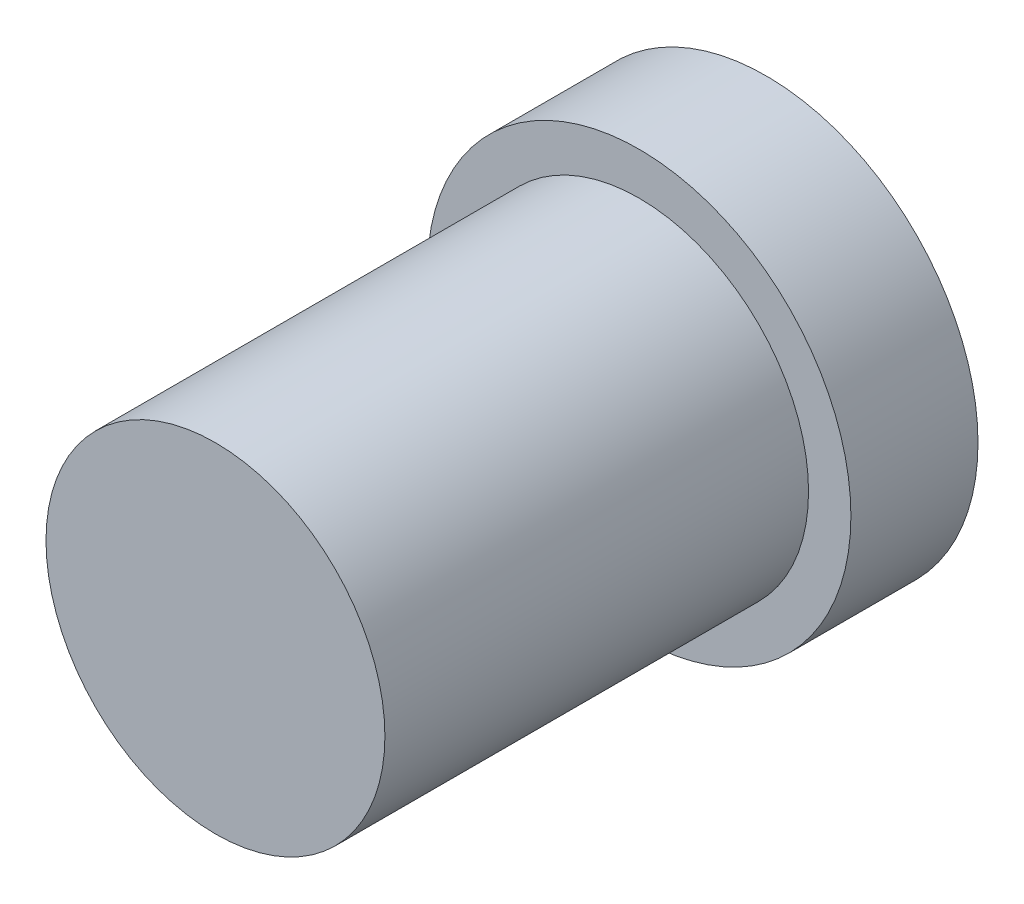
SolidWorks part; units mm, degrees
ref_plane "Front Plane" through (0, 0, 0) normal (0, 0, 1) x (1, 0, 0)
ref_plane "Top Plane" through (0, 0, 0) normal (0, 1, 0) x (1, 0, 0)
ref_plane "Right Plane" through (0, 0, 0) normal (1, 0, 0) x (0, 0, -1)
sketch "Sketch1" plane through (0, 0, 0) normal (0, 0, 1) x (1, 0, 0)
  circle A0 centre (0, 0) radius 5
  dimension "D1" = 10
extrude "Boss-Extrude1" add sketch "Sketch1" along normal blind 3
sketch "Sketch2" plane through (0, 0, 3) normal (0, 0, 1) x (1, 0, 0)
  circle A0 centre (0, 0) radius 4
  dimension "D1" = 8
extrude "Boss-Extrude2" add sketch "Sketch2" along normal blind 10
